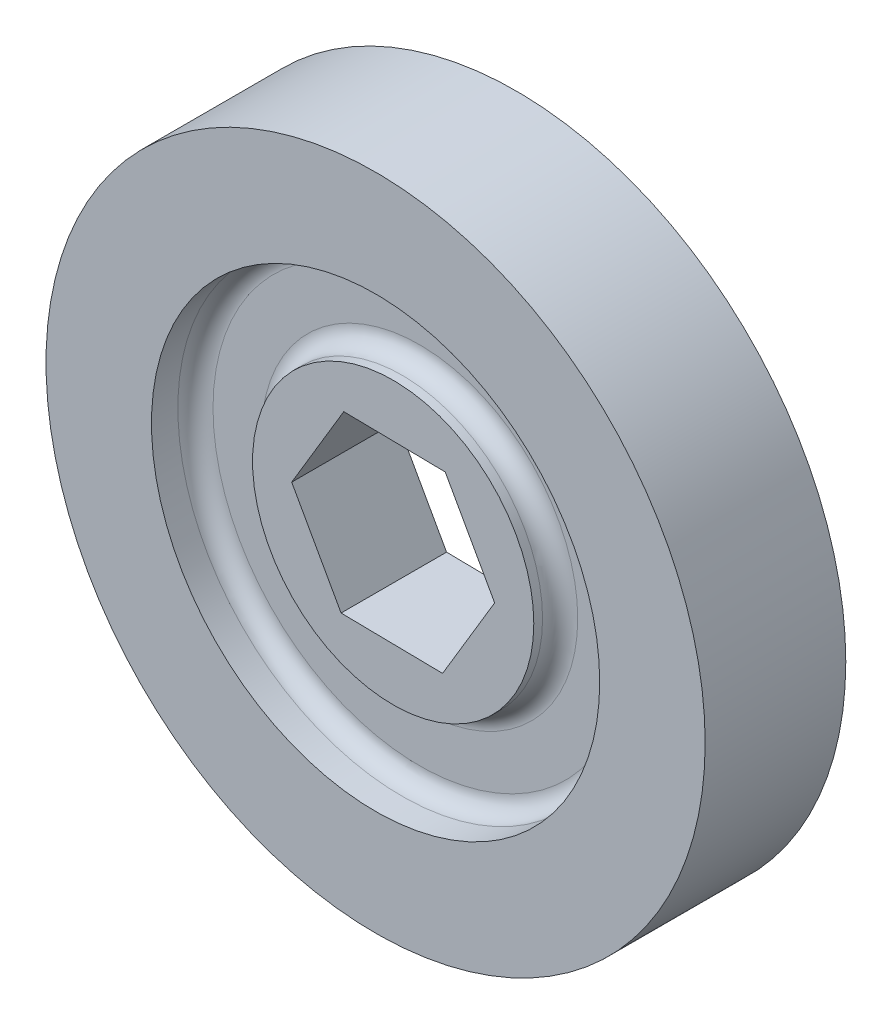
SolidWorks part; units mm, degrees
ref_plane "Front Plane" through (0, 0, 0) normal (0, 0, 1) x (1, 0, 0)
ref_plane "Top Plane" through (0, 0, 0) normal (0, 1, 0) x (1, 0, 0)
ref_plane "Right Plane" through (0, 0, 0) normal (1, 0, 0) x (0, 0, -1)
sketch "Sketch1" plane through (0, 0, 0) normal (0, 0, 1) x (1, 0, 0)
  line L1 (3.5692, -6.405) -> (7.3315, -0.1114)
  line L2 (7.3315, -0.1114) -> (3.7623, 6.2935)
  line L3 (3.7623, 6.2935) -> (-3.5692, 6.405)
  line L4 (-3.5692, 6.405) -> (-7.3315, 0.1114)
  line L5 (-7.3315, 0.1114) -> (-3.7623, -6.2935)
  line L6 (-3.7623, -6.2935) -> (3.5692, -6.405)
  circle A0 centre (0, 0) radius 23.8125
  circle A1 centre (0, 0) radius 6.35 construction
  dimension "D1" = 47.625
  dimension "D2" = 12.7
extrude "Boss-Extrude1" add sketch "Sketch1" along normal blind 10.16
sketch "Sketch2" plane through (0, 0, 10.16) normal (0, 0, 1) x (1, 0, 0)
  circle A0 centre (0, 0) radius 10.16
  circle A1 centre (0, 0) radius 16.1925
  dimension "D1" = 20.32
  dimension "D2" = 32.385
extrude "Cut-Extrude1" cut sketch "Sketch2" against normal blind 3.175
sketch "Sketch3" plane through (0, 0, 0) normal (0, 0, -1) x (-1, 0, 0)
  circle A0 centre (0, 0) radius 16.1925
  circle A1 centre (0, 0) radius 10.16
  dimension "D1" = 32.385
  dimension "D2" = 20.32
extrude "Cut-Extrude2" cut sketch "Sketch3" against normal blind 3.175
sketch "Sketch4" plane through (0, 0, 0) normal (0, 0, -1) x (-1, 0, 0)
  circle A0 centre (0, 0) radius 10.16
extrude "Cut-Extrude3" cut sketch "Sketch4" against normal blind 1.27
sketch "Sketch7" plane through (0, 0, 10.16) normal (0, 0, 1) x (1, 0, 0)
  circle A0 centre (0, 0) radius 10.16
extrude "Cut-Extrude5" cut sketch "Sketch7" against normal blind 1.27
fillet "Fillet1" radius 1.27 4 edges at (-10.16, 0, 3.175) (-16.1925, 0, 3.175) (10.16, 0, 6.985) (16.1925, 0, 6.985)
